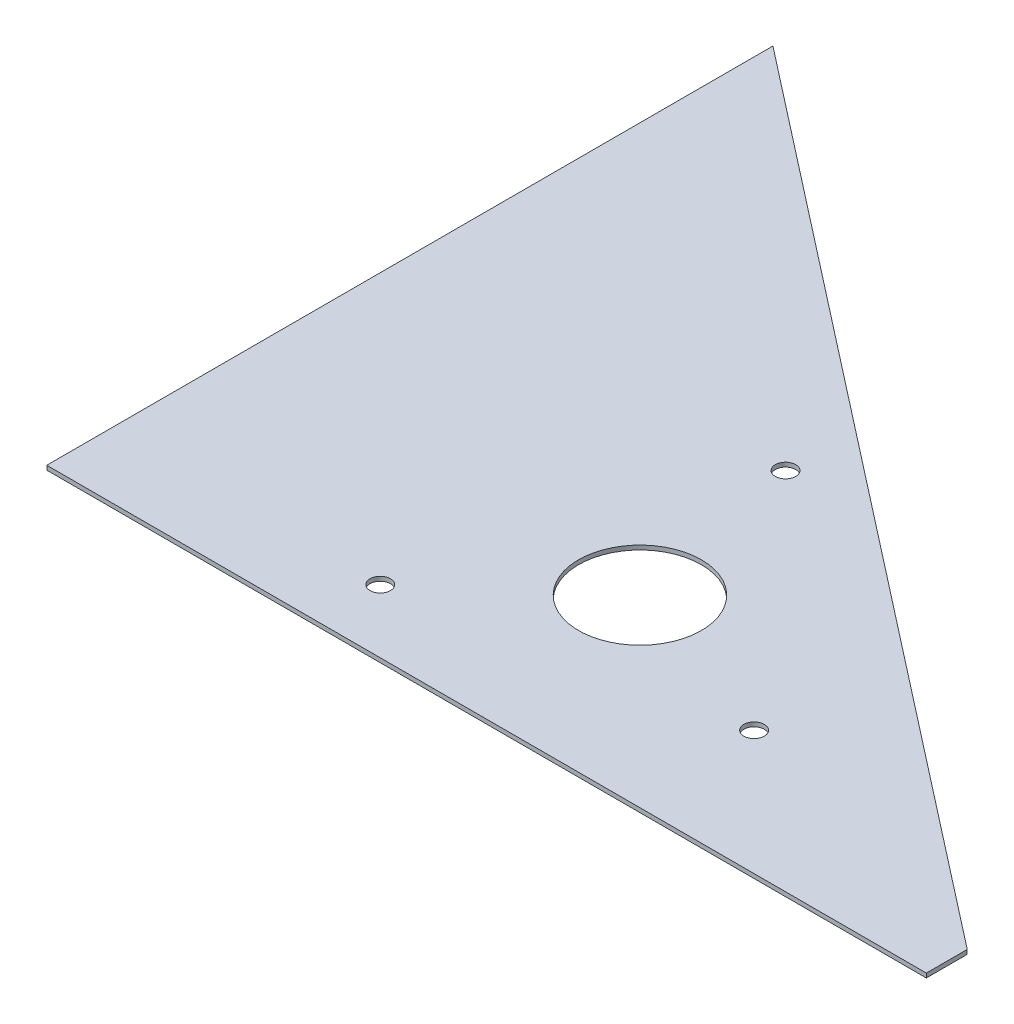
SolidWorks part; units mm, degrees
ref_plane "Front Plane" through (0, 0, 0) normal (0, 0, 1) x (1, 0, 0)
ref_plane "Top Plane" through (0, 0, 0) normal (0, 1, 0) x (1, 0, 0)
ref_plane "Right Plane" through (0, 0, 0) normal (1, 0, 0) x (0, 0, -1)
sketch "Sketch1" plane through (0, 0, 0) normal (0, 1, 0) x (1, 0, 0)
  line L0 (0, 450.85) -> (0, 0)
  line L1 (0, 0) -> (546.1, 0)
  line L2 (546.1, 0) -> (546.1, 25.4)
  line L3 (546.1, 25.4) -> (0, 450.85)
  dimension "D1" = 450.85
  dimension "D2" = 546.1
  dimension "D3" = 25.4
extrude "Boss-Extrude1" add sketch "Sketch1" along normal blind 2.6568
ref_plane "Plane1" through (220.1389, 0, -282.5663) normal (0.6146, 0, -0.7889) x (-0.7889, 0, -0.6146)
sketch "Sketch2" plane through (0, 0, 0) normal (0, -1, 0) x (1, 0, 0)
  line L0 (546.1, 0) -> (546.1, -25.4) construction
  line L1 (0, 0) -> (546.1, 0) construction
  circle A0 centre (254, -114.3) radius 38.1
  dimension "D1" = 76.2
  dimension "D2" = 292.1
  dimension "D3" = 114.3
extrude "Cut-Extrude1" cut sketch "Sketch2" against normal through all
sketch "Sketch3" plane through (0, 2.6568, 0) normal (0, 1, 0) x (1, 0, 0)
  line L0 (254, 228.6) -> (254, 0) construction
  line L1 (139.7, 114.3) -> (368.3, 114.3) construction
  line L2 (254, 114.3) -> (529.4177, 19.4661) construction
  circle A0 centre (254, 114.3) radius 101.6 construction
  circle A1 centre (254, 114.3) radius 114.3 construction
  circle A2 centre (362.0728, 77.0876) radius 6.35
  circle A3 centre (167.7367, 39.3125) radius 6.35
  circle A4 centre (232.1905, 226.5) radius 6.35
  point P18 (254, 114.3)
  dimension "D1" = 203.2
  dimension "D2" = 228.6
  dimension "D4" = 12.7
  dimension "D3" = 19
extrude "Cut-Extrude2" cut sketch "Sketch3" against normal through all
